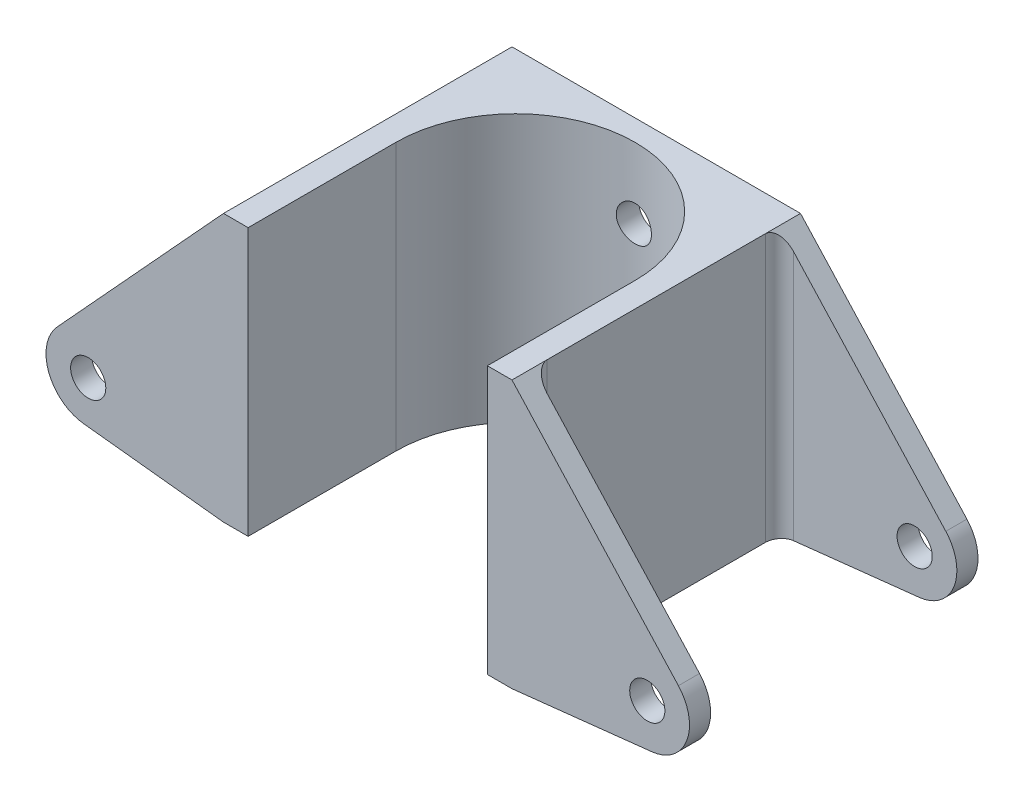
SolidWorks part; units mm, degrees
ref_plane "Front Plane" through (0, 0, 0) normal (0, 0, 1) x (1, 0, 0)
ref_plane "Top Plane" through (0, 0, 0) normal (0, 1, 0) x (1, 0, 0)
ref_plane "Right Plane" through (0, 0, 0) normal (1, 0, 0) x (0, 0, -1)
sketch "Sketch1" plane through (0, 0, 0) normal (0, 0, 1) x (1, 0, 0)
  line L0 (-20.5, 0) -> (-40.3808, 2.1805)
  line L1 (-20.5, 38) -> (20.5, 38)
  line L2 (-20.5, 38) -> (-20.5, 0) construction
  line L3 (-20.5, 0) -> (20.5, 0)
  line L4 (20.5, 38) -> (20.5, 0) construction
  line L5 (-44.1497, 12.199) -> (-20.5, 38)
  line L6 (0, -55) -> (0, 55) construction
  line L7 (20.5, 0) -> (40.3808, 2.1805)
  line L8 (44.1497, 12.199) -> (20.5, 38)
  arc A0 (-40.3808, 2.1805) -> (-44.1497, 12.199) centre (-39.7266, 8.1447) cw
  arc A1 (40.3808, 2.1805) -> (44.1497, 12.199) centre (39.7266, 8.1447) ccw
  dimension "D3" = 6
  dimension "D1" = 38
  dimension "D2" = 41
  dimension "D4" = 35
  dimension "D5" = 20
extrude "Boss-Extrude1" add sketch "Sketch1" along normal blind 41
sketch "Sketch3" plane through (0, 0, 0) normal (0, 1, 0) x (1, 0, 0)
  line L0 (20.5, -41) -> (20.5, 0) construction
  line L1 (20.5, -3) -> (45.7266, -3)
  line L2 (20.5, -3) -> (20.5, -38)
  line L3 (20.5, -38) -> (45.7266, -38)
  line L4 (45.7266, -3) -> (45.7266, -38)
  line L5 (45.7266, -41) -> (45.7266, 0) construction
  line L6 (44.1497, -41) -> (20.5, -41) construction
  line L8 (0, -55) -> (0, 55) construction
  line L9 (-20.5, -3) -> (-20.5, -38)
  line L10 (-20.5, -38) -> (-45.7266, -38)
  line L11 (-45.7266, -3) -> (-45.7266, -38)
  line L12 (-20.5, -3) -> (-45.7266, -3)
  line L13 (-20.5, 0) -> (-44.1497, 0) construction
  dimension "D1" = 3
  dimension "D2" = 3
extrude "Cut-Extrude2" cut sketch "Sketch3" against normal through all and the other way through all
sketch "Sketch4" plane through (0, 0, 0) normal (0, -1, 0) x (1, 0, 0)
  line L0 (-20.5, 41) -> (20.5, 41) construction
  line L2 (-17, 20) -> (-17, 41)
  line L3 (-17, 41) -> (17, 41)
  line L4 (17, 20) -> (17, 41)
  line L5 (-20.5, 0) -> (20.5, 0) construction
  arc A0 (-17, 20) -> (17, 20) centre (0, 20) ccw
  dimension "D1" = 17
  dimension "D2" = 20
extrude "Cut-Extrude3" cut sketch "Sketch4" against normal through all
sketch "Sketch5" plane through (0, 0, 0) normal (0, 0, -1) x (-1, 0, 0)
  line L0 (0, 28) -> (0, 10) construction
  line L1 (0, 0) -> (0, 38) construction
  line L2 (-20.5, 38) -> (20.5, 38) construction
  circle A0 centre (0, 28) radius 2.5
  circle A1 centre (0, 10) radius 2.5
  point P10 (0, 19)
  point P11 (0, 19)
  dimension "D1" = 5
  dimension "D2" = 10
extrude "Cut-Extrude4" cut sketch "Sketch5" against normal through all
sketch "Sketch6" plane through (0, 0, 41) normal (0, 0, 1) x (1, 0, 0)
  circle A0 centre (-39.7266, 8.1447) radius 2.5
  arc A1 (-44.1497, 12.199) -> (-40.3808, 2.1805) centre (-39.7266, 8.1447) ccw construction
  dimension "D1" = 5
extrude "Cut-Extrude5" cut sketch "Sketch6" against normal through all contours A0
mirror "Mirror1" about plane through (0, 0, 0) normal (1, 0, 0) of "Cut-Extrude5"
fillet "Fillet1" radius 2 4 edges at (20.5, 19, 38) (20.5, 19, 3) (-20.5, 19, 38) (-20.5, 19, 3)
